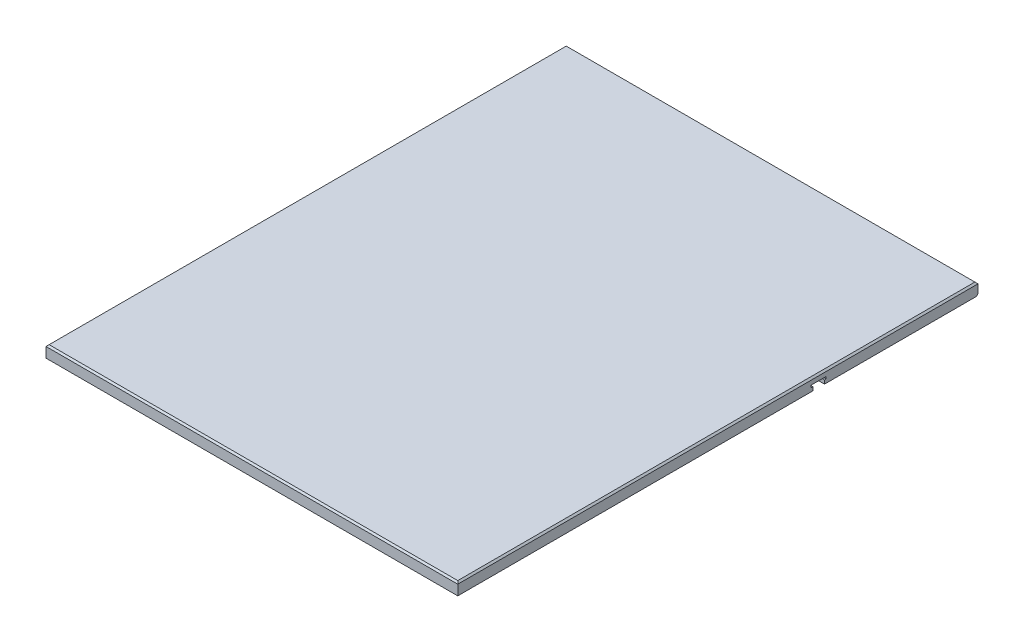
SolidWorks part; units mm, degrees
material "Oak"
ref_plane "Front Plane" through (0, 0, 0) normal (0, 0, 1) x (1, 0, 0)
ref_plane "Top Plane" through (0, 0, 0) normal (0, 1, 0) x (1, 0, 0)
ref_plane "Right Plane" through (0, 0, 0) normal (1, 0, 0) x (0, 0, -1)
sketch "Sketch1" plane through (0, 0, 0) normal (0, 1, 0) x (1, 0, 0)
  line L1 (0, 0) -> (669.8488, 0)
  line L2 (0, 0) -> (0, 846.328)
  line L3 (0, 846.328) -> (669.8488, 846.328)
  line L4 (669.8488, 0) -> (669.8488, 846.328)
  dimension "D1" = 846.328
  dimension "D2" = 669.8488
extrude "Boss-Extrude1" add sketch "Sketch1" along normal blind 19.05
chamfer "Chamfer1" distance 2.54 angle 45 4 edges at (334.9244, 19.05, -846.328) (669.8488, 19.05, -423.164) (334.9244, 19.05, 0) (0, 19.05, -423.164)
chamfer "Chamfer2" distance 2.54 angle 45 1 edges at (334.9244, 0, -846.328)
sketch "Sketch3" plane through (0, 0, 0) normal (-1, 0, 0) x (0, 0, 1)
  line L5 (-846.328, 16.51) -> (-846.328, 2.54)
  line L6 (-846.328, 2.54) -> (-843.788, 0)
  line L7 (-843.788, 0) -> (0, 0)
  line L8 (0, 0) -> (0, 16.51)
  line L9 (0, 16.51) -> (-846.328, 16.51)
  line L10 (-846.328, 16.51) -> (-846.328, 2.54)
  line L11 (-846.328, 2.54) -> (-843.788, 0)
  line L12 (-843.788, 0) -> (0, 0)
  line L13 (0, 0) -> (0, 16.51)
  line L14 (0, 16.51) -> (-846.328, 16.51)
  line L17 (-599.2978, 5.9753) -> (-599.2978, 9.5313)
  line L18 (-596.6308, 5.9753) -> (-599.2978, 5.9753)
  line L19 (-596.6308, 0) -> (-596.6308, 5.9753)
  line L20 (-577.5808, 5.9753) -> (-577.5808, 0)
  line L21 (-574.9138, 9.5313) -> (-574.9138, 5.9753)
  line L22 (-574.9138, 5.9753) -> (-577.5808, 5.9753)
  line L23 (-599.2978, 9.5313) -> (-574.9138, 9.5313)
  line L24 (-587.1058, 10.86) -> (-587.1058, -6.3519) construction
  line L25 (-596.6308, 0) -> (-577.5808, 0)
  dimension "D2" = 9.5313
  dimension "D3" = 5.9753
  dimension "D4" = 574.9138
  dimension "D5" = 24.384
  dimension "D6" = 19.05
  dimension "D1" = 0
extrude "Cut-Extrude2" cut sketch "Sketch3" against normal through all contours L24 L23 L17 L18 L19 L12 | L23 L24 L25 L20 L22 L21
